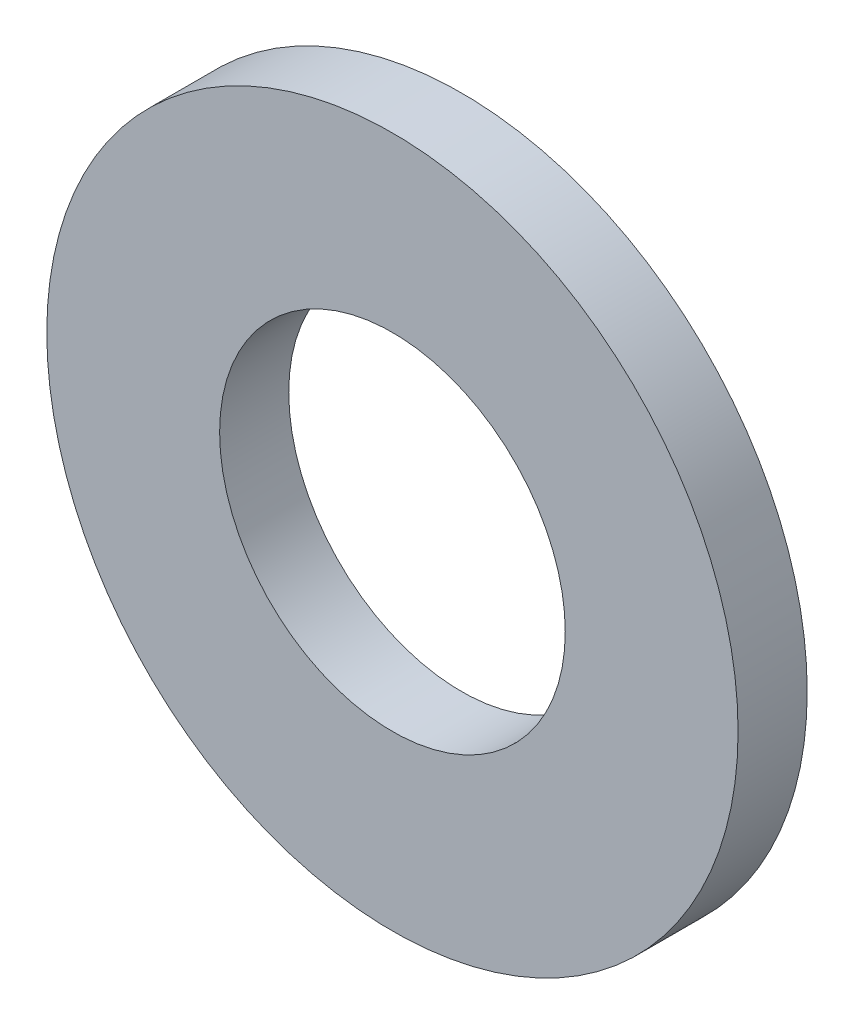
SolidWorks part; units mm, degrees
ref_plane "Front" through (0, 0, 0) normal (0, 0, 1) x (1, 0, 0)
ref_plane "Top" through (0, 0, 0) normal (0, 1, 0) x (1, 0, 0)
ref_plane "Right" through (0, 0, 0) normal (1, 0, 0) x (0, 0, -1)
sketch "Sketch1" plane through (0, 0, 0) normal (0, 0, 1) x (1, 0, 0)
  circle A0 centre (0, 0) radius 5
  circle A1 centre (0, 0) radius 10
  circle A3 centre (0, 0) radius 5 construction
  dimension "D1" = 5
extrude "Boss-Extrude1" add sketch "Sketch1" along normal blind 2
